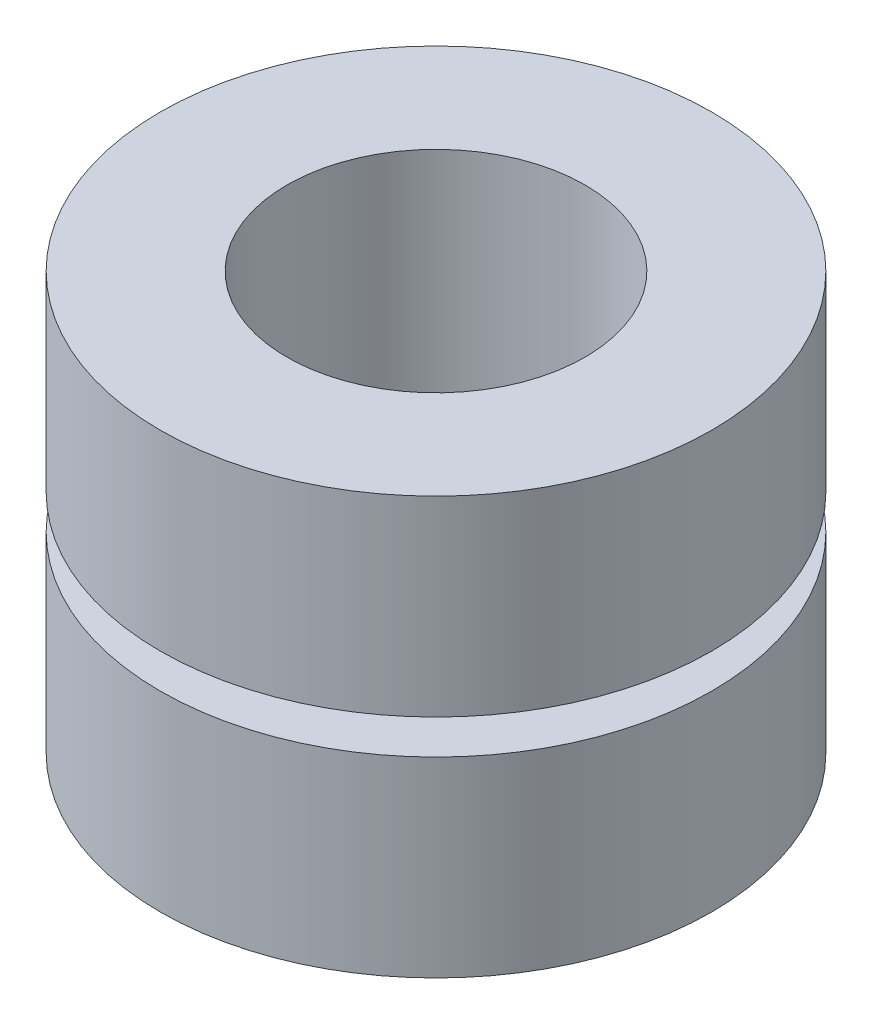
SolidWorks part; units mm, degrees
material "NEOPRENE"
ref_plane "Front Plane" through (0, 0, 0) normal (0, 0, 1) x (1, 0, 0)
ref_plane "Top Plane" through (0, 0, 0) normal (0, 1, 0) x (1, 0, 0)
ref_plane "Right Plane" through (0, 0, 0) normal (1, 0, 0) x (0, 0, -1)
sketch "Sketch1" plane through (0, 0, 0) normal (0, 0, 1) x (1, 0, 0)
  line L0 (0, 0) -> (0, 26.9358) construction
  line L1 (2.5146, 0) -> (2.5146, 7.0358)
  line L2 (2.5146, 7.0358) -> (4.6482, 7.0358)
  line L3 (4.6482, 7.0358) -> (4.6482, 3.81)
  line L4 (2.5146, 0) -> (4.6482, 0)
  line L5 (4.6482, 0) -> (4.6482, 3.2258)
  line L6 (4.5759, 3.81) -> (2.8194, 3.81)
  line L7 (2.8194, 3.81) -> (2.8194, 3.2258)
  line L8 (2.8194, 3.2258) -> (4.6482, 3.2258)
  line L9 (4.6482, 3.81) -> (4.5759, 3.81)
  point P12 (2.8194, 3.5179)
  dimension "D1" = 7.0358
  dimension "D2" = 2.5146
  dimension "D3" = 2.1336
  dimension "D4" = 3.2258
  dimension "D5" = 3.2258
  dimension "D6" = 2.8194
revolve "Revolve1" add sketch "Sketch1" angle 360 about L0
